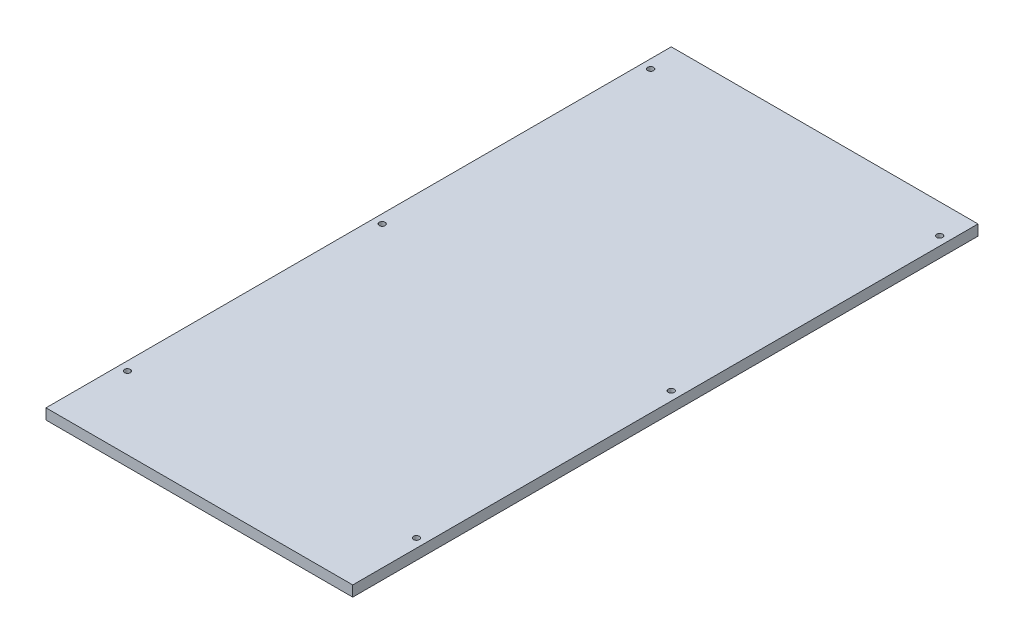
SolidWorks part; units mm, degrees
ref_plane "Front" through (0, 0, 0) normal (0, 0, 1) x (1, 0, 0)
ref_plane "Top" through (0, 0, 0) normal (0, 1, 0) x (1, 0, 0)
ref_plane "Right" through (0, 0, 0) normal (1, 0, 0) x (0, 0, -1)
sketch "Sketch1" plane through (0, 0, 0) normal (0, 1, 0) x (1, 0, 0)
  line L1 (-260, 0) -> (260, 0)
  line L2 (-260, 0) -> (-260, -1060)
  line L3 (-260, -1060) -> (260, -1060)
  line L4 (260, 0) -> (260, -1060)
  dimension "D1" = 520
  dimension "D2" = 1060
extrude "Boss-Extrude1" add sketch "Sketch1" along normal blind 18
sketch "Sketch2" plane through (0, 18, 0) normal (0, 1, 0) x (1, 0, 0)
  line L0 (260, 0) -> (-260, 0) construction
  line L1 (260, -1060) -> (260, 0) construction
  line L2 (0, 56.5758) -> (0, -69.0226) construction
  circle A0 centre (245, -50) radius 5
  circle A1 centre (-245, -50) radius 5
  circle A2 centre (245, -505) radius 5
  circle A3 centre (245, -937) radius 5
  circle A4 centre (-245, -937) radius 5
  circle A5 centre (-245, -505) radius 5
  dimension "D3" = 10
  dimension "D4" = 455
  dimension "D1" = 50
  dimension "D2" = 15
  dimension "D5" = 887
extrude "Cut-Extrude1" cut sketch "Sketch2" against normal through all
